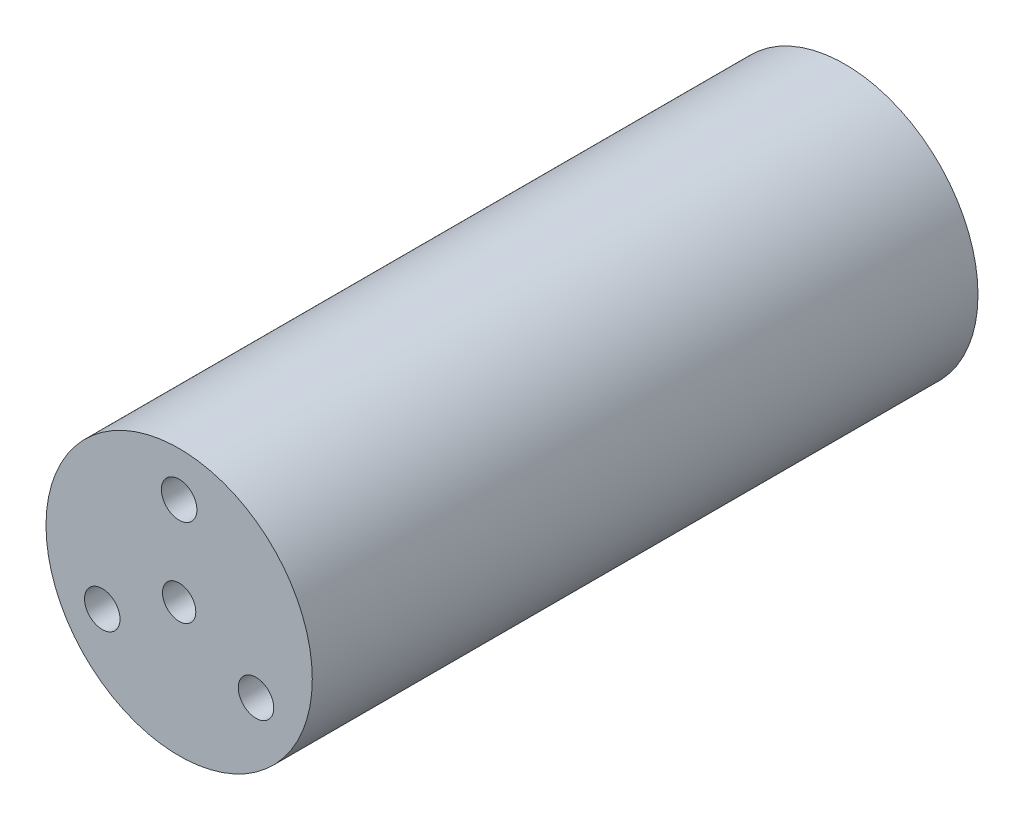
SolidWorks part; units mm, degrees
ref_plane "Plan de face" through (0, 0, 0) normal (0, 0, 1) x (1, 0, 0)
ref_plane "Plan de dessus" through (0, 0, 0) normal (0, 1, 0) x (1, 0, 0)
ref_plane "Plan de droite" through (0, 0, 0) normal (1, 0, 0) x (0, 0, -1)
sketch "Esquisse1" plane through (0, 0, 0) normal (0, 0, 1) x (1, 0, 0)
  circle A0 centre (0, 0) radius 6
  circle A1 centre (0, 0) radius 0.75
  dimension "D1" = 12
  dimension "D2" = 1.5
extrude "Extrusion1" add sketch "Esquisse1" along normal blind 30
hole_wizard "Trou taraudé M21" positions "Esquisse3" profile "Esquisse2" tap size "M2" standard "ISO"
sketch "Esquisse3" plane through (0, 0, 30) normal (0, 0, 1) x (1, 0, 0)
  point P0 (0, 4)
  dimension "D1" = 4
sketch "Esquisse2" plane through (0, 4, 30) normal (1, 0, 0) x (0, -1, 0)
  line L0 (0, 0) -> (0, 6.4807)
  line L1 (0, 6.4807) -> (0.8, 6)
  line L2 (0.8, 6) -> (0.8, 0)
  line L5 (0.8, 0) -> (0, 0)
  line L10 (0, 6.4807) -> (-0.8, 6) construction
  line L11 (0, -6.35) -> (0, 107.95) construction
  dimension "Diamètre du trou pour taraudage" = 1.6
  dimension "Profondeur du trou pour taraudage" = 6
  dimension "Angle de pointe" = 118
cosmetic thread "Filetage de perçage1" parameters "D1"=4, "D2"=2
pattern_circular "Répétition circulaire1" count 3 every 120 about axis through (0, 0, 0) along (0, 0, 1) of "Trou taraudé M21"
sketch "Esquisse4" plane through (0, 0, 0) normal (0, 0, -1) x (-1, 0, 0)
  circle A0 centre (-1.2755, -3.7912) radius 1
  dimension "D1" = 2
  dimension "D2" = 4
extrude "Extrusion2" cut sketch "Esquisse4" against normal blind 2
pattern_circular "Répétition circulaire2" count 2 every 180 about axis through (0, 0, 0) along (0, 0, 1) of "Extrusion2"
